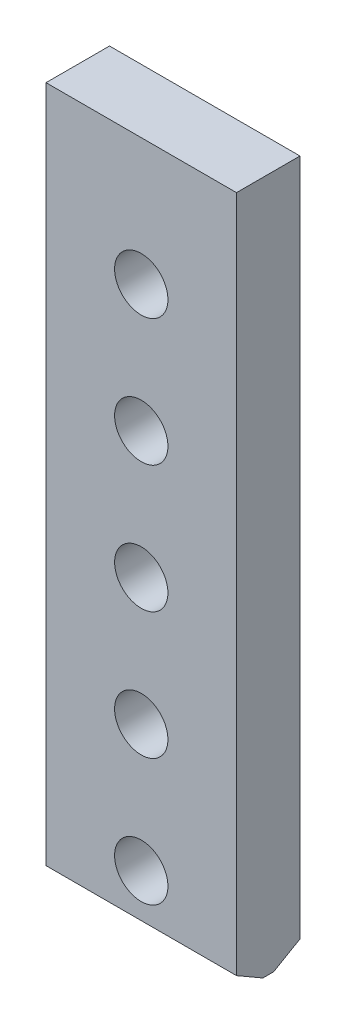
SolidWorks part; units mm, degrees
material "Простая углеродистая сталь"
ref_plane "Спереди" through (0, 0, 0) normal (0, 0, 1) x (1, 0, 0)
ref_plane "Сверху" through (0, 0, 0) normal (0, 1, 0) x (1, 0, 0)
ref_plane "Справа" through (0, 0, 0) normal (1, 0, 0) x (0, 0, -1)
sketch "Эскиз1" plane through (0, 0, 0) normal (0, 0, 1) x (1, 0, 0)
  line L1 (0, 0) -> (75, 0)
  line L2 (0, 0) -> (0, 273)
  line L3 (0, 273) -> (75, 273)
  line L4 (75, 0) -> (75, 273)
  point P5 (37.5, 273)
  dimension "D1" = 273
  dimension "D2" = 75
extrude "Бобышка-Вытянуть1" add sketch "Эскиз1" along normal blind 25
sketch "Эскиз2" plane through (0, 0, 25) normal (0, 0, 1) x (1, 0, 0)
  line L0 (0, 0) -> (75, 0) construction
  line L1 (75, 0) -> (75, 273) construction
  circle A0 centre (37.5, 23) radius 10.5
  circle A1 centre (37.5, 73) radius 10.5
  circle A2 centre (37.5, 123) radius 10.5
  circle A3 centre (37.5, 173) radius 10.5
  circle A4 centre (37.5, 223) radius 10.5
  dimension "D1" = 5
  dimension "D2" = 23
  dimension "D3" = 37.5
  dimension "D4" = 21
extrude "Вырез-Вытянуть1" cut sketch "Эскиз2" against normal through all
chamfer "Фаска1" distance 6 angle 60 1 edges at (37.5, 0, 0)
chamfer "Фаска2" distance 6 angle 60 1 edges at (37.5, 0, 25)
